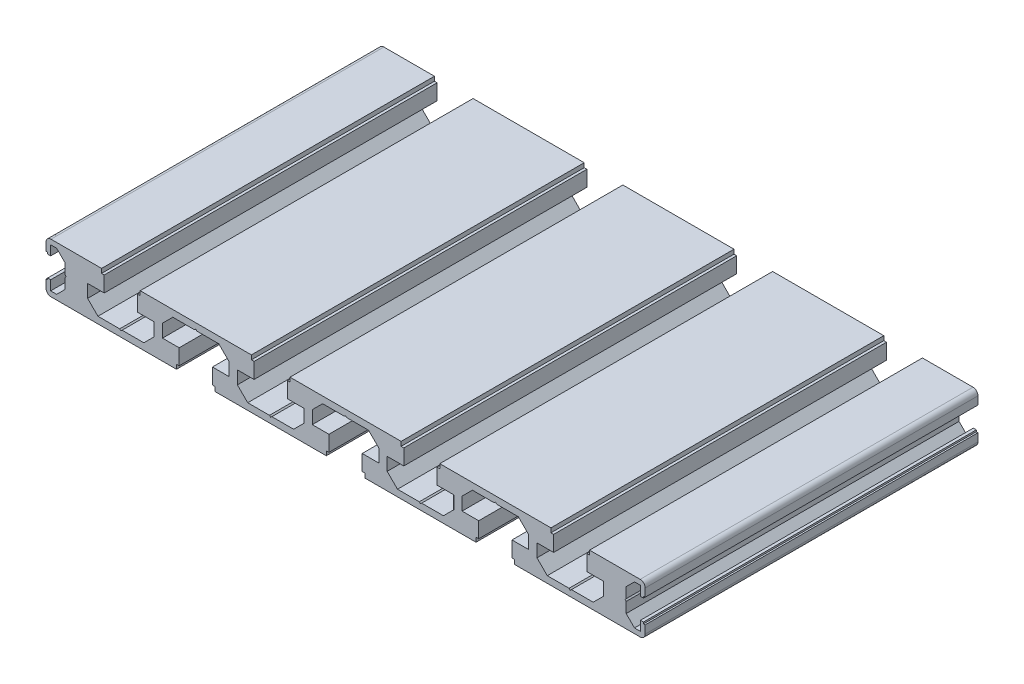
SolidWorks part; units mm, degrees
material "АД31Т ГОСТ 4784-97"
ref_plane "Спереди" through (0, 0, 0) normal (0, 0, 1) x (1, 0, 0)
ref_plane "Сверху" through (0, 0, 0) normal (0, 1, 0) x (1, 0, 0)
ref_plane "Справа" through (0, 0, 0) normal (1, 0, 0) x (0, 0, -1)
sketch "Model" plane through (0, 0, 0) normal (0, 0, 1) x (1, 0, 0)
  line L0 (0, 25.2738) -> (0, -16.7073) construction
  line L1 (-12.5, 11.1) -> (-12, 11.1)
  line L2 (-11, 0) -> (26.7, 0)
  line L3 (26.7, 1.3) -> (26.7, 0)
  line L4 (38.3, 1.3) -> (38.3, 0)
  line L5 (-12, 11.1) -> (-12, 10.6)
  line L6 (-12.5, 3.9) -> (-12, 3.9)
  line L7 (-12, 3.9) -> (-12, 4.4)
  line L8 (-11.1, 13.5) -> (-9.3, 13.5)
  line L9 (-9.3, 13.5) -> (-6.8, 11)
  line L10 (-6.8, 11) -> (-6.8, 4)
  line L11 (-6.8, 4) -> (-9.3, 1.5)
  line L12 (-9.3, 1.5) -> (-11.1, 1.5)
  line L13 (60.8, 15) -> (94.2, 15)
  line L14 (94.2, 15) -> (94.2, 13.7)
  line L15 (94.2, 13.7) -> (95, 13.7)
  line L16 (95, 13.7) -> (95, 9)
  line L17 (95, 9) -> (90, 9)
  line L18 (90, 9) -> (90, 5.1)
  line L19 (90, 5.1) -> (93.1, 2)
  line L20 (93.1, 2) -> (106.9, 2)
  line L21 (106.9, 2) -> (110, 5.1)
  line L22 (110, 5.1) -> (110, 9)
  line L23 (110, 9) -> (105, 9)
  line L24 (105, 9) -> (105, 13.7)
  line L25 (105, 13.7) -> (105.8, 13.7)
  line L26 (105.8, 13.7) -> (105.8, 15)
  line L27 (105.8, 15) -> (139.2, 15)
  line L28 (38.3, 0) -> (71.7, 0)
  line L29 (71.7, 0) -> (71.7, 1.3)
  line L30 (71.7, 1.3) -> (72.5, 1.3)
  line L31 (72.5, 1.3) -> (72.5, 6)
  line L32 (72.5, 6) -> (67.5, 6)
  line L33 (67.5, 6) -> (67.5, 9.9)
  line L34 (67.5, 9.9) -> (70.6, 13)
  line L35 (70.6, 13) -> (84.4, 13)
  line L36 (84.4, 13) -> (87.5, 9.9)
  line L37 (87.5, 9.9) -> (87.5, 6)
  line L38 (87.5, 6) -> (82.5, 6)
  line L39 (82.5, 6) -> (82.5, 1.3)
  line L40 (82.5, 1.3) -> (83.3, 1.3)
  line L41 (83.3, 1.3) -> (83.3, 0)
  line L42 (83.3, 0) -> (116.7, 0)
  line L43 (116.7, 0) -> (116.7, 1.3)
  line L44 (116.7, 1.3) -> (117.5, 1.3)
  line L45 (117.5, 1.3) -> (117.5, 6)
  line L46 (117.5, 6) -> (112.5, 6)
  line L47 (112.5, 6) -> (112.5, 9.9)
  line L48 (112.5, 9.9) -> (115.6, 13)
  line L49 (115.6, 13) -> (129.4, 13)
  line L50 (129.4, 13) -> (132.5, 9.9)
  line L51 (132.5, 9.9) -> (132.5, 6)
  line L52 (132.5, 6) -> (127.5, 6)
  line L53 (127.5, 6) -> (127.5, 1.3)
  line L54 (127.5, 1.3) -> (128.3, 1.3)
  line L55 (128.3, 1.3) -> (128.3, 0)
  line L56 (128.3, 0) -> (166, 0)
  line L57 (139.2, 15) -> (139.2, 13.7)
  line L58 (139.2, 13.7) -> (140, 13.7)
  line L59 (140, 13.7) -> (140, 9)
  line L60 (140, 9) -> (135, 9)
  line L61 (135, 9) -> (135, 5.1)
  line L62 (135, 5.1) -> (138.1, 2)
  line L63 (138.1, 2) -> (151.9, 2)
  line L64 (151.9, 2) -> (155, 5.1)
  line L65 (155, 5.1) -> (155, 9)
  line L66 (155, 9) -> (150, 9)
  line L67 (150, 9) -> (150, 13.7)
  line L68 (150, 13.7) -> (150.8, 13.7)
  line L69 (150.8, 13.7) -> (150.8, 15)
  line L70 (150.8, 15) -> (166, 15)
  line L71 (10, 15) -> (10, 0) construction
  line L72 (32.5, 15) -> (32.5, 0) construction
  line L73 (-12.5, 7.5) -> (167.3, 7.5) construction
  line L74 (77.5, 33.5149) -> (77.5, -14.526) construction
  line L75 (167.5, 1.5) -> (167.5, 3.9)
  line L76 (166.1, 4.4) -> (167, 4.4)
  line L77 (166.1, 10.6) -> (167, 10.6)
  line L78 (166.1, 4.4) -> (166.1, 1.5)
  line L79 (166.1, 13.5) -> (166.1, 10.6)
  line L80 (167.5, 11.1) -> (167.5, 13.5)
  line L81 (164.3, 1.5) -> (166.1, 1.5)
  line L82 (161.8, 4) -> (164.3, 1.5)
  line L83 (161.8, 11) -> (161.8, 4)
  line L84 (164.3, 13.5) -> (161.8, 11)
  line L85 (166.1, 13.5) -> (164.3, 13.5)
  line L86 (167, 3.9) -> (167, 4.4)
  line L87 (167.5, 3.9) -> (167, 3.9)
  line L88 (167, 11.1) -> (167, 10.6)
  line L89 (167.5, 11.1) -> (167, 11.1)
  line L90 (55, 0) -> (55, 15) construction
  line L91 (100, 0) -> (100, 15) construction
  line L92 (122.5, 15) -> (122.5, 0) construction
  line L97 (49.2, 13.7) -> (50, 13.7)
  line L98 (49.2, 15) -> (49.2, 13.7)
  line L99 (60.8, 13.7) -> (60, 13.7)
  line L100 (60.8, 15) -> (60.8, 13.7)
  line L101 (48.1, 2) -> (45, 5.1)
  line L102 (61.9, 2) -> (65, 5.1)
  line L103 (61.9, 2) -> (48.1, 2)
  line L104 (45, 9) -> (45, 5.1)
  line L105 (65, 9) -> (65, 5.1)
  line L106 (60, 9) -> (65, 9)
  line L107 (60, 13.7) -> (60, 9)
  line L108 (50, 9) -> (45, 9)
  line L109 (50, 13.7) -> (50, 9)
  line L111 (38.3, 1.3) -> (37.5, 1.3)
  line L113 (26.7, 1.3) -> (27.5, 1.3)
  line L115 (39.4, 13) -> (42.5, 9.9)
  line L116 (25.6, 13) -> (22.5, 9.9)
  line L117 (25.6, 13) -> (39.4, 13)
  line L118 (42.5, 6) -> (42.5, 9.9)
  line L119 (22.5, 6) -> (22.5, 9.9)
  line L120 (27.5, 6) -> (22.5, 6)
  line L121 (27.5, 1.3) -> (27.5, 6)
  line L122 (37.5, 6) -> (42.5, 6)
  line L123 (37.5, 1.3) -> (37.5, 6)
  line L124 (4.2, 13.7) -> (5, 13.7)
  line L125 (4.2, 15) -> (4.2, 13.7)
  line L126 (15.8, 13.7) -> (15, 13.7)
  line L127 (15.8, 15) -> (15.8, 13.7)
  line L128 (3.1, 2) -> (0, 5.1)
  line L129 (16.9, 2) -> (20, 5.1)
  line L130 (16.9, 2) -> (3.1, 2)
  line L131 (15.8, 15) -> (49.2, 15)
  line L132 (0, 9) -> (0, 5.1)
  line L133 (20, 9) -> (20, 5.1)
  line L134 (15, 9) -> (20, 9)
  line L135 (15, 13.7) -> (15, 9)
  line L136 (5, 9) -> (0, 9)
  line L137 (5, 13.7) -> (5, 9)
  line L138 (-12.5, 11.1) -> (-12.5, 13.5)
  line L139 (-11.1, 13.5) -> (-11.1, 10.6)
  line L143 (-11.1, 4.4) -> (-11.1, 1.5)
  line L144 (-11.1, 10.6) -> (-12, 10.6)
  line L145 (-11.1, 4.4) -> (-12, 4.4)
  line L156 (-11, 15) -> (4.2, 15)
  line L157 (-12.5, 1.5) -> (-12.5, 3.9)
  arc A0 (167.5, 13.5) -> (166, 15) centre (166, 13.5) ccw
  arc A1 (166, 0) -> (167.5, 1.5) centre (166, 1.5) ccw
  arc A3 (-11, 0) -> (-12.5, 1.5) centre (-11, 1.5) cw
  arc A4 (-12.5, 13.5) -> (-11, 15) centre (-11, 13.5) cw
  point P62 (10, 2)
  point P80 (32.5, 13)
  point P108 (0, 0)
  point P110 (55, 2)
  dimension "D4" = 0.8
  dimension "D22" = 1.5
  dimension "D2" = 15
  dimension "D3" = 1.3
  dimension "D6" = 5
  dimension "D7" = 6
  dimension "D8" = 13.8
  dimension "D9" = 10
  dimension "D10" = 7
  dimension "D11" = 22.5
  dimension "D12" = 45
  dimension "D13" = 12
  dimension "D14" = 7.5
  dimension "D15" = 45
  dimension "D16" = 6.2
  dimension "D17" = 0.5
  dimension "D18" = 0.5
  dimension "D19" = 1.4
  dimension "D20" = 5.7
  dimension "D21" = 7
  dimension "D23" = 40
  dimension "D24" = 180
extrude "Бобышка-Вытянуть1" add sketch "Model" along normal blind 100
sketch "Эскиз1" plane through (0, 0, 100) normal (0, 0, 1) x (1, 0, 0)
  line L0 (-6.8, 7.8536) -> (-6.4464, 7.5)
  line L1 (-6.8, 11) -> (-6.8, 4) construction
  line L2 (-6.4464, 7.5) -> (-6.8, 7.1464)
  line L3 (-6.8, 7.1464) -> (-6.8, 7.8536)
  line L4 (9.6464, 2) -> (10, 1.6464)
  line L5 (16.9, 2) -> (3.1, 2) construction
  line L6 (10, 1.6464) -> (10.3536, 2)
  line L7 (10.3536, 2) -> (9.6464, 2)
  line L8 (32.1464, 13) -> (32.5, 13.3536)
  line L9 (25.6, 13) -> (39.4, 13) construction
  line L10 (32.5, 13.3536) -> (32.8536, 13)
  line L11 (32.8536, 13) -> (32.1464, 13)
  line L12 (54.6464, 2) -> (55, 1.6464)
  line L13 (61.9, 2) -> (48.1, 2) construction
  line L14 (55, 1.6464) -> (55.3536, 2)
  line L15 (55.3536, 2) -> (54.6464, 2)
  line L16 (77.1464, 13) -> (77.5, 13.3536)
  line L17 (70.6, 13) -> (84.4, 13) construction
  line L18 (77.5, 13.3536) -> (77.8536, 13)
  line L19 (77.8536, 13) -> (77.1464, 13)
  line L20 (99.6464, 2) -> (100, 1.6464)
  line L21 (106.9, 2) -> (93.1, 2) construction
  line L22 (100, 1.6464) -> (100.3536, 2)
  line L23 (100.3536, 2) -> (99.6464, 2)
  line L24 (122.1464, 13) -> (122.5, 13.3536)
  line L25 (115.6, 13) -> (129.4, 13) construction
  line L26 (122.5, 13.3536) -> (122.8536, 13)
  line L27 (122.8536, 13) -> (122.1464, 13)
  line L28 (144.6464, 2) -> (145, 1.6464)
  line L29 (151.9, 2) -> (138.1, 2) construction
  line L30 (145, 1.6464) -> (145.3536, 2)
  line L31 (145.3536, 2) -> (144.6464, 2)
  line L32 (161.8, 7.8536) -> (161.4464, 7.5)
  line L33 (161.8, 4) -> (161.8, 11) construction
  line L34 (161.4464, 7.5) -> (161.8, 7.1464)
  line L35 (161.8, 7.1464) -> (161.8, 7.8536)
  point P45 (32.5, 13)
  point P46 (10, 2)
  point P47 (77.5, 13)
  point P48 (100, 2)
  point P49 (145, 2)
  point P50 (0, 0)
  point P51 (-6.8, 7.5)
  point P53 (161.8, 7.5)
  point P56 (55, 2)
  point P57 (122.5, 13)
  dimension "D1" = 0.5
extrude "Вырез-Вытянуть1" cut sketch "Эскиз1" against normal up to surface (100 mm away) up to face at (77.5, 7.7239, 0)
